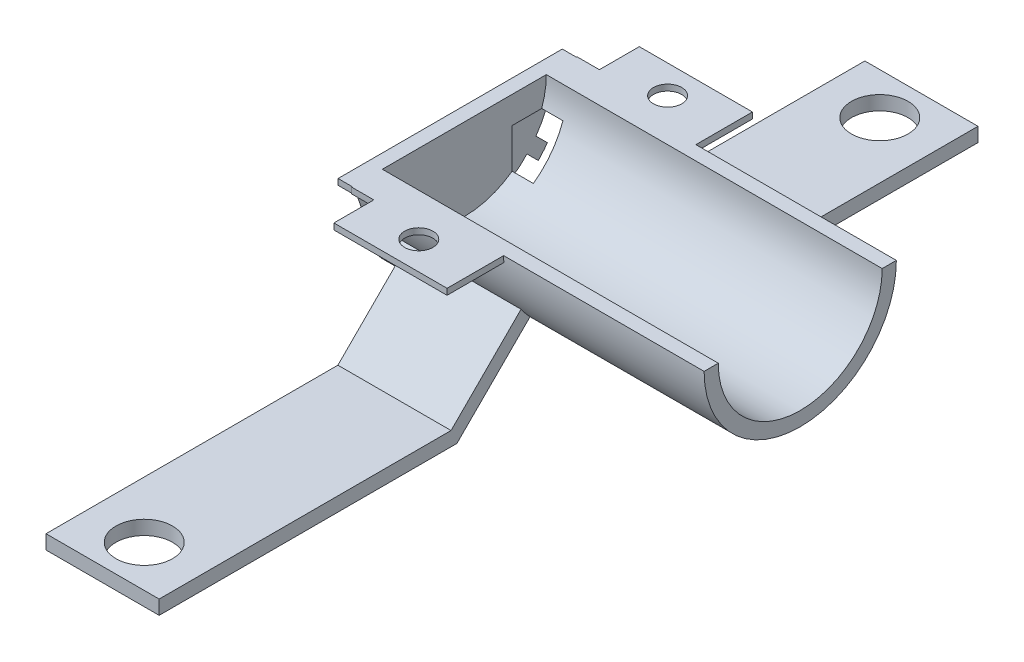
SolidWorks part; units mm, degrees
ref_plane "Front" through (0, 0, 0) normal (0, 0, 1) x (1, 0, 0)
ref_plane "Top" through (0, 0, 0) normal (0, 1, 0) x (1, 0, 0)
ref_plane "Right" through (0, 0, 0) normal (1, 0, 0) x (0, 0, -1)
sketch "Sketch4" plane through (0, 0, 0) normal (1, 0, 0) x (0, 0, -1)
  line L0 (-95.0344, -14.331) -> (-28.1991, -14.331)
  line L1 (-28.1991, -14.331) -> (-9.5344, 4.3337)
  line L3 (-11.5143, 6.844) -> (-29.5143, -11.156)
  line L4 (-29.5143, -11.156) -> (-95.0344, -11.156)
  line L5 (-95.0344, -11.156) -> (-95.0344, -14.331)
  line L6 (-17.7065, 16.9401) -> (25.4435, 16.9401)
  line L7 (3.8685, 64.8542) -> (3.8685, -48.2941) construction
  line L8 (35.9362, -14.331) -> (17.2715, 4.3337)
  line L9 (19.2513, 6.844) -> (37.2513, -11.156)
  line L10 (35.9362, -14.331) -> (88.7715, -14.331)
  line L11 (88.7715, -14.331) -> (88.7715, -11.156)
  line L12 (88.7715, -11.156) -> (37.2513, -11.156)
  line L13 (-17.7065, 16.9401) -> (-30.4065, 16.9401)
  line L14 (-30.4065, 16.9401) -> (-30.4065, 15.5698)
  line L15 (-30.4065, 15.5698) -> (-17.6629, 15.5698)
  line L16 (25.4435, 16.9401) -> (38.1435, 16.9401)
  line L17 (38.1435, 16.9401) -> (38.1435, 15.5698)
  line L18 (38.1435, 15.5698) -> (25.4, 15.5698)
  line L22 (24.0651, 16.9047) -> (25.4435, 16.9401)
  line L23 (-17.6629, 15.5698) -> (-16.5295, 16.7032)
  line L24 (-16.5295, 16.7032) -> (-17.7065, 16.9401)
  line L25 (25.4, 15.5698) -> (24.0651, 16.9047)
  circle A0 centre (3.8685, 16.9401) radius 18.4
  circle A1 centre (3.8685, 16.9401) radius 21.575
  dimension "D4" = 3.175
  dimension "D8" = 36.8
  dimension "D1" = 3.175
  dimension "D2" = 3.175
  dimension "D3" = 18
  dimension "D5" = 85.5
  dimension "D6" = 71.5
  dimension "D10" = 12.7
  dimension "D11" = 12.7
extrude "Boss-Extrude2" add sketch "Sketch4" along normal blind 25.4
sketch "Sketch5" plane through (0, -11.156, 0) normal (0, 1, 0) x (1, 0, 0)
  line L0 (0, -29.5143) -> (0, -95.0344) construction
  line L1 (25.4, -95.0344) -> (0, -95.0344) construction
  circle A0 centre (12.7, -85.6844) radius 6.35
  dimension "D3" = 12.7
  dimension "D1" = 12.7
  dimension "D2" = 9.35
extrude "Cut-Extrude3" cut sketch "Sketch5" against normal blind 25.4
sketch "Sketch6" plane through (0, -11.156, 0) normal (0, 1, 0) x (1, 0, 0)
  line L0 (25.4, 88.7715) -> (25.4, 37.2513) construction
  line L1 (25.4, 88.7715) -> (0, 88.7715) construction
  circle A0 centre (12.7, 79.4215) radius 6.35
  dimension "D3" = 12.7
  dimension "D1" = 12.7
  dimension "D2" = 9.35
extrude "Cut-Extrude4" cut sketch "Sketch6" against normal blind 25.4
sketch "Sketch7" plane through (0, 16.9401, 0) normal (0, 1, 0) x (1, 0, 0)
  line L0 (25.4, -30.4065) -> (0, -30.4065) construction
  circle A0 centre (12.7, -24.0565) radius 3.175
  dimension "D1" = 6.35
  dimension "D2" = 6.35
  dimension "D3" = 12.7
extrude "Cut-Extrude5" cut sketch "Sketch7" against normal blind 3.175
sketch "Sketch8" plane through (0, 16.9401, 0) normal (0, 1, 0) x (1, 0, 0)
  line L0 (0, 22.2685) -> (0, 38.1435) construction
  line L1 (25.4, 38.1435) -> (0, 38.1435) construction
  circle A0 centre (12.7, 31.7935) radius 3.175
  dimension "D1" = 6.35
  dimension "D2" = 12.7
  dimension "D3" = 6.35
extrude "Cut-Extrude6" cut sketch "Sketch8" against normal blind 3.175
sketch "Sketch10" plane through (0, 0, 0) normal (-1, 0, 0) x (0, 0, 1)
  line L0 (-59.4519, 16.9401) -> (-22.2685, 16.9401)
  line L1 (21.4471, 16.9401) -> (51.7148, 16.9401)
  circle A0 centre (-3.8685, 16.9401) radius 25.3156
  circle A1 centre (-3.8685, 16.9401) radius 55.5834
  arc M6 (13.7999, 4.5584) -> (17.6629, 15.5698) centre (-3.8685, 16.9401) ccw
  line M9 (30.4065, 16.9401) -> (14.5315, 16.9401)
  arc M10 (14.5315, 16.9401) -> (-22.2685, 16.9401) centre (-3.8685, 16.9401) cw
  line M11 (-22.2685, 16.9401) -> (-38.1435, 16.9401)
  arc M14 (-25.4, 15.5698) -> (-21.537, 4.5584) centre (-3.8685, 16.9401) ccw
  arc M20 (-19.5175, 2.0877) -> (11.7804, 2.0877) centre (-3.8685, 16.9401) ccw
extrude "Boss-Extrude3" add sketch "Sketch10" along normal blind 5 contours A1 M11 M14 M20 M6 M9 M10
sketch "Sketch11" plane through (-5, 0, 0) normal (-1, 0, 0) x (0, 0, 1)
  line L0 (-29.1842, 16.9401) -> (21.2978, 16.9401)
  circle A0 centre (-3.8685, 16.9401) radius 25.1663
extrude "Boss-Extrude4" add sketch "Sketch11" along normal blind 3.175
sketch "Sketch12" plane through (0, 0, -88.7715) normal (0, 0, -1) x (-1, 0, 0)
  line L1 (0.2375, 10.87) -> (6.5875, 10.87)
  line L2 (0.2375, 10.87) -> (0.2375, -1.83)
  line L3 (0.2375, -1.83) -> (6.5875, -1.83)
  line L4 (6.5875, 10.87) -> (6.5875, -1.83)
  dimension "D1" = 6.35
  dimension "D2" = 12.7
  dimension "D3" = 1.5875
extrude "Cut-Extrude7" cut sketch "Sketch12" against normal blind 74.175
sketch "Sketch13" plane through (25.4, 0, 0) normal (1, 0, 0) x (0, 0, -1)
  line L0 (-14.5315, 16.9401) -> (22.2685, 16.9401) construction
  line L1 (-17.7065, 16.9401) -> (25.4435, 16.9401)
  circle A0 centre (3.8685, 16.9401) radius 21.575
  circle A1 centre (3.8685, 16.9401) radius 18.2879
  arc A2 (-11.7804, 2.0877) -> (19.5175, 2.0877) centre (3.8685, 16.9401) ccw construction
  arc M2 (-11.7804, 2.0877) -> (19.5175, 2.0877) centre (3.8685, 16.9401) ccw
  arc M8 (21.537, 4.5584) -> (25.4, 15.5698) centre (3.8685, 16.9401) ccw
  line M11 (38.1435, 16.9401) -> (22.2685, 16.9401)
  arc M12 (22.2685, 16.9401) -> (-14.5315, 16.9401) centre (3.8685, 16.9401) cw
  line M13 (-14.5315, 16.9401) -> (-30.4065, 16.9401)
  arc M16 (-17.6629, 15.5698) -> (-13.7999, 4.5584) centre (3.8685, 16.9401) ccw
extrude "Boss-Extrude5" add sketch "Sketch13" along normal blind 45 contours A0 M13 M16 M2 M8 M11 M12
